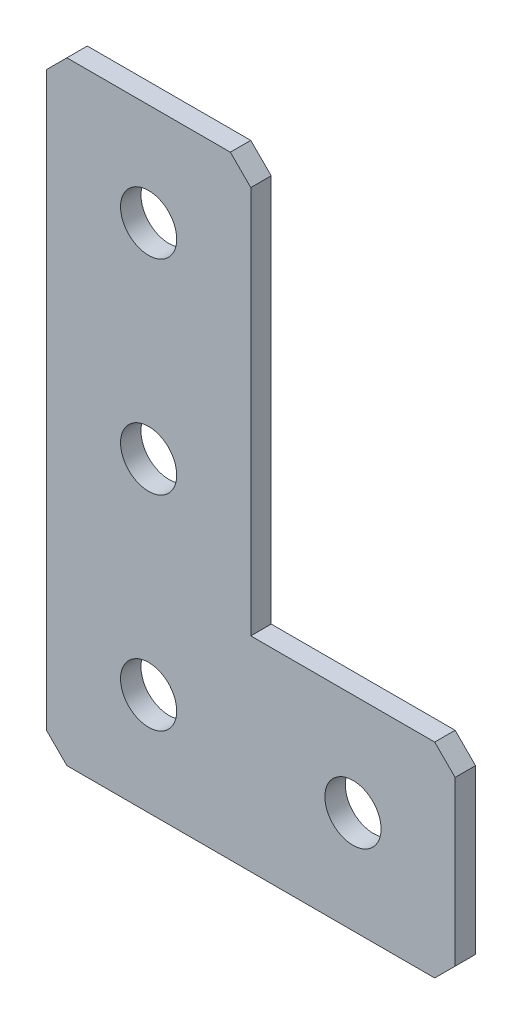
SolidWorks part; units mm, degrees
material "Простая углеродистая сталь"
ref_plane "Спереди(Плоскость XY)" through (0, 0, 0) normal (0, 0, 1) x (1, 0, 0)
ref_plane "Сверху(Плоскость XZ)" through (0, 0, 0) normal (0, 1, 0) x (1, 0, 0)
ref_plane "Справа(Плоскость ZY)" through (0, 0, 0) normal (1, 0, 0) x (0, 0, -1)
sketch "Эскиз1" plane through (0, 0, 0) normal (0, 0, -1) x (1, 0, 0)
  line L0 (0, 0) -> (0, 60)
  line L1 (0, 60) -> (40, 60)
  line L2 (40, 60) -> (40, 40)
  line L3 (40, 40) -> (20, 40)
  line L4 (20, 40) -> (20, 0)
  line L5 (20, 0) -> (0, 0)
  dimension "D1" = 60
  dimension "D2" = 20
  dimension "D3" = 20
  dimension "D4" = 20
extrude "Бобышка-Вытянуть1" add sketch "Эскиз1" along normal blind 2
hole_wizard "Отверстие с зазором M51" positions "Эскиз2" profile "Эскиз3" hole size "M5" standard "DIN" end condition through all
sketch "Эскиз2" plane through (0, 0, -2) normal (0, 0, -1) x (1, 0, 0)
  line L0 (10, 0) -> (10, 60) construction
  line L1 (0, 0) -> (20, 0) construction
  line L2 (40, 60) -> (0, 60) construction
  line L3 (40, 50) -> (0, 50) construction
  line L4 (40, 40) -> (40, 60) construction
  line L5 (0, 60) -> (0, 0) construction
  point P0 (30, 50)
  point P2 (10, 50)
  point P4 (10, 30)
  point P6 (10, 10)
  dimension "D1" = 20
  dimension "D2" = 20
  dimension "D3" = 20
  dimension "D4" = 10
sketch "Эскиз3" plane through (30, -50, -2) normal (1, 0, 0) x (0, 1, 0)
  line L0 (0, 0) -> (0, 2)
  line L1 (0, 2) -> (2.75, 2)
  line L2 (2.75, 2) -> (2.75, 0)
  line L5 (2.75, 0) -> (0, 0)
  line L11 (0, -6.35) -> (0, 107.95) construction
  dimension "Диаметр сквозного отверстия" = 5.5
  dimension "Глубина сквозного отверстия" = 2
chamfer "Фаска1" distance 2 angle 45 5 edges at (0, 0, -1) (20, 0, -1) (40, -40, -1) (40, -60, -1) (0, -60, -1)
